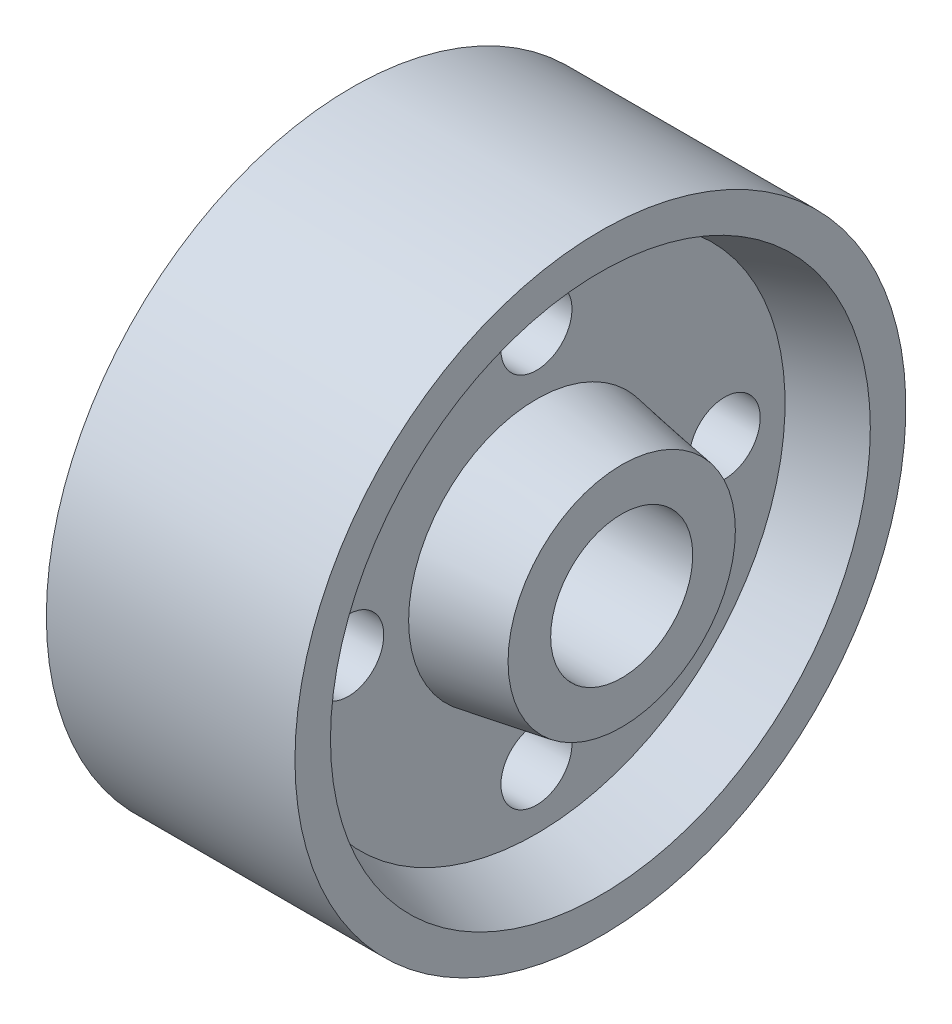
SolidWorks part; units mm, degrees
ref_plane "Front Plane" through (0, 0, 0) normal (0, 0, 1) x (1, 0, 0)
ref_plane "Top Plane" through (0, 0, 0) normal (0, 1, 0) x (1, 0, 0)
ref_plane "Right Plane" through (0, 0, 0) normal (1, 0, 0) x (0, 0, -1)
sketch "Sketch1" plane through (0, 0, 0) normal (0, 0, 1) x (1, 0, 0)
  line L0 (-54.3218, 0) -> (54.3218, 0) construction
  line L1 (0, 0) -> (0, 16)
  line L2 (0, 16) -> (12, 18)
  line L3 (12, 18) -> (12, 35)
  line L4 (12, 35) -> (3, 38)
  line L5 (3, 38) -> (3, 43)
  line L6 (3, 43) -> (38, 43)
  line L7 (20.5, 43) -> (20.5, 0) construction
  line L8 (41, 0) -> (41, 16)
  line L9 (41, 16) -> (29, 18)
  line L10 (29, 18) -> (29, 35)
  line L11 (29, 35) -> (38, 38)
  line L12 (38, 38) -> (38, 43)
  line L13 (0, 0) -> (41, 0)
  point P4 (0, 0)
  dimension "D1" = 32
  dimension "D2" = 36
  dimension "D3" = 70
  dimension "D4" = 76
  dimension "D5" = 86
  dimension "D6" = 12
  dimension "D7" = 17.5
  dimension "D8" = 3
  dimension "D9" = 20.5
revolve "Revolve1" add sketch "Sketch1" angle 360 about L13
sketch "Sketch2" plane through (0, 0, 0) normal (-1, 0, 0) x (0, 0, 1)
  circle A0 centre (0, 0) radius 10
  circle A1 centre (0, 0) radius 26.5 construction
  circle A2 centre (0, 26.5) radius 5
  circle A3 centre (26.5, 0) radius 5
  circle A4 centre (0, -26.5) radius 5
  circle A5 centre (-26.5, 0) radius 5
  point P7 (-27.7917, -1.255)
  point P14 (0, 0)
  dimension "D1" = 20
  dimension "D2" = 53
  dimension "D3" = 10
  dimension "D4" = 4
extrude "Cut-Extrude1" cut sketch "Sketch2" against normal through all
